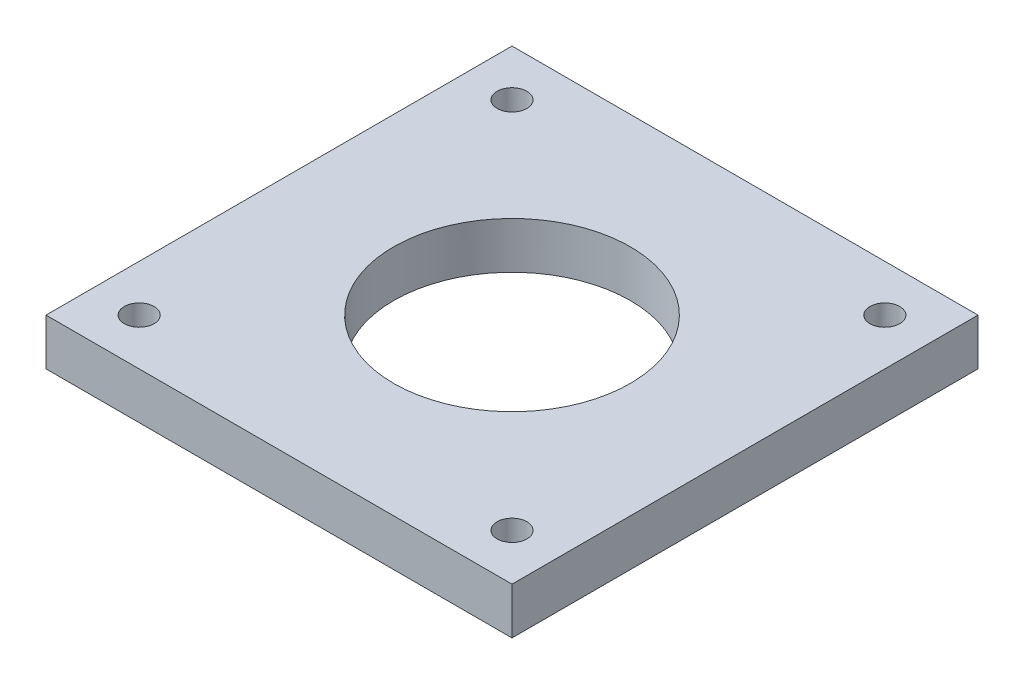
SolidWorks part; units mm, degrees
ref_plane "Front" through (0, 0, 0) normal (0, 0, 1) x (1, 0, 0)
ref_plane "Top" through (0, 0, 0) normal (0, 1, 0) x (1, 0, 0)
ref_plane "Right" through (0, 0, 0) normal (1, 0, 0) x (0, 0, -1)
sketch "Sketch1" plane through (0, 0, 0) normal (0, 1, 0) x (1, 0, 0)
  line L1 (-25, -25) -> (25, -25)
  line L2 (-25, -25) -> (-25, 25)
  line L3 (-25, 25) -> (25, 25)
  line L4 (25, -25) -> (25, 25)
  line L5 (-25, -25) -> (25, 25) construction
  line L6 (-25, 25) -> (25, -25) construction
  point P0 (0, 0)
  dimension "D1" = 50
  dimension "D2" = 50
extrude "Extrude1" add sketch "Sketch1" along normal blind 5
hole_wizard "M3 Clearance Hole1" positions "3DSketch1" profile "Sketch2" hole size "M3" standard "Ansi Metric"
sketch3d "3DSketch1"
  line L0 (-25, 5, -25) -> (-25, 5, 25) construction
  line L1 (-25, 5, 25) -> (25, 5, 25) construction
  point P0 (-20, 5, 20)
  dimension "D1" = 5
  dimension "D2" = 5
sketch "Sketch2" plane through (-20, 5, 20) normal (1, 0, 0) x (0, 0, 1)
  line L0 (0, 0) -> (0, 6.9614)
  line L1 (0, 6.9614) -> (1.6, 6)
  line L2 (1.6, 6) -> (1.6, 0)
  line L5 (1.6, 0) -> (0, 0)
  line L10 (0, 6.9614) -> (-1.6, 6) construction
  line L11 (0, -6.35) -> (0, 107.95) construction
  dimension "Hole Dia." = 3.2
  dimension "Hole Depth" = 6
  dimension "Drill Angle" = 118
sketch "Sketch3" plane through (0, 5, 0) normal (0, 1, 0) x (-1, 0, 0)
  line L0 (20, 20) -> (20, -29.1402) construction
  line L1 (20, 20) -> (-30.1021, 20) construction
pattern_linear "LPattern1" count 2 spacing 40 along (0, 0, -1) count 2 spacing 40 along (1, 0, 0) of "M3 Clearance Hole1"
hole_wizard "1 (1) Diameter Hole1" positions "3DSketch3" profile "Sketch5" hole size "1" standard "Ansi Inch"
sketch3d "3DSketch3"
  line L0 (25, 5, -25) -> (-25, 5, -25) construction
  line L1 (-25, 5, -25) -> (-25, 5, 25) construction
  point P0 (0, 5, 0)
  dimension "D1" = 25
  dimension "D2" = 25
sketch "Sketch5" plane through (0, 5, 0) normal (1, 0, 0) x (0, 0, 1)
  line L0 (0, 0) -> (0, 13.6309)
  line L1 (0, 13.6309) -> (12.7, 6)
  line L2 (12.7, 6) -> (12.7, 0)
  line L5 (12.7, 0) -> (0, 0)
  line L10 (0, 13.6309) -> (-12.7, 6) construction
  line L11 (0, -6.35) -> (0, 107.95) construction
  dimension "Hole Dia." = 25.4
  dimension "Hole Depth" = 6
  dimension "Drill Angle" = 118
